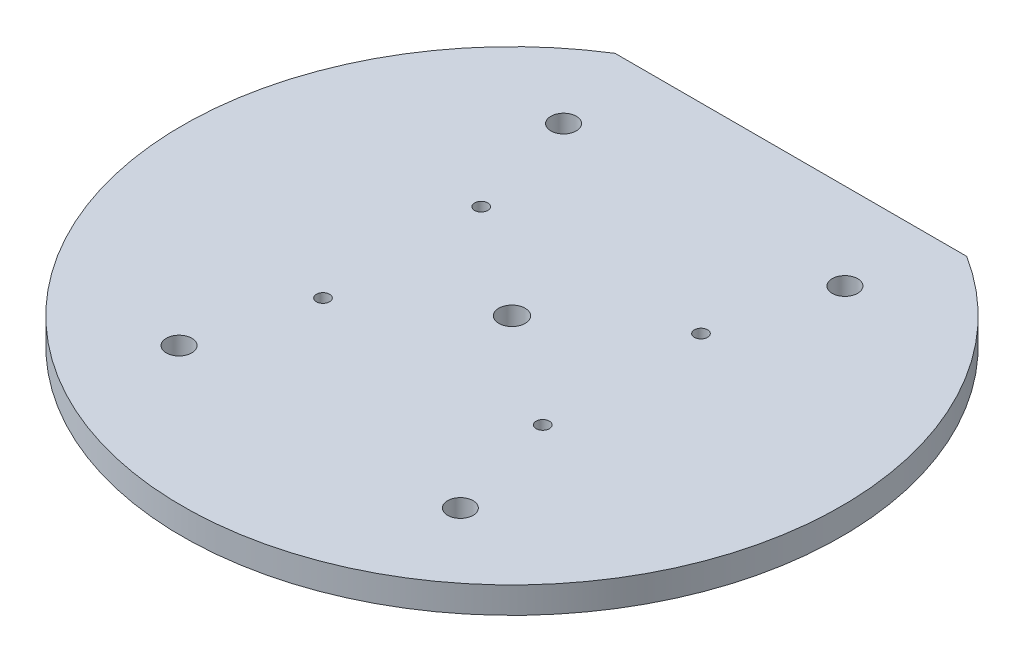
SolidWorks part; units mm, degrees
ref_plane "Front Plane" through (0, 0, 0) normal (0, 0, 1) x (1, 0, 0)
ref_plane "Top Plane" through (0, 0, 0) normal (0, 1, 0) x (1, 0, 0)
ref_plane "Right Plane" through (0, 0, 0) normal (1, 0, 0) x (0, 0, -1)
sketch "Sketch1" plane through (0, 0, 0) normal (0, 1, 0) x (1, 0, 0)
  circle A0 centre (0, 0) radius 75
  dimension "D1" = 150
extrude "Boss-Extrude1" add sketch "Sketch1" along normal blind 6
sketch "Sketch2" plane through (0, 6, 0) normal (0, 1, 0) x (1, 0, 0)
  line L0 (-88.6759, 0) -> (98.4211, 0) construction
  line L1 (0, 81.3901) -> (0, -84.4157) construction
  line L2 (-40, 63.4429) -> (40, 63.4429) construction
  line L3 (-40, 63.4429) -> (40, 63.4429)
  line L4 (40, 63.4429) -> (40, 86.7466)
  line L5 (40, 86.7466) -> (-40, 86.7466)
  line L6 (-40, 86.7466) -> (-40, 63.4429)
  circle A0 centre (-32, 43.7429) radius 2.9
  circle A1 centre (0, 0) radius 75 construction
  circle A2 centre (32, 43.7429) radius 2.9
  circle A3 centre (0, 0) radius 3
  circle A4 centre (-32, -43.7429) radius 2.9
  circle A5 centre (32, -43.7429) radius 2.9
  circle A6 centre (25, 18) radius 1.5
  circle A7 centre (-25, 18) radius 1.5
  circle A8 centre (-25, -18) radius 1.5
  circle A9 centre (25, -18) radius 1.5
  dimension "D1" = 5.8
  dimension "D5" = 6
  dimension "D6" = 3
  dimension "D2" = 32
  dimension "D3" = 80
  dimension "D4" = 19.7
  dimension "D7" = 25
  dimension "D8" = 18
extrude "Cut-Extrude1" cut sketch "Sketch2" against normal blind 6
